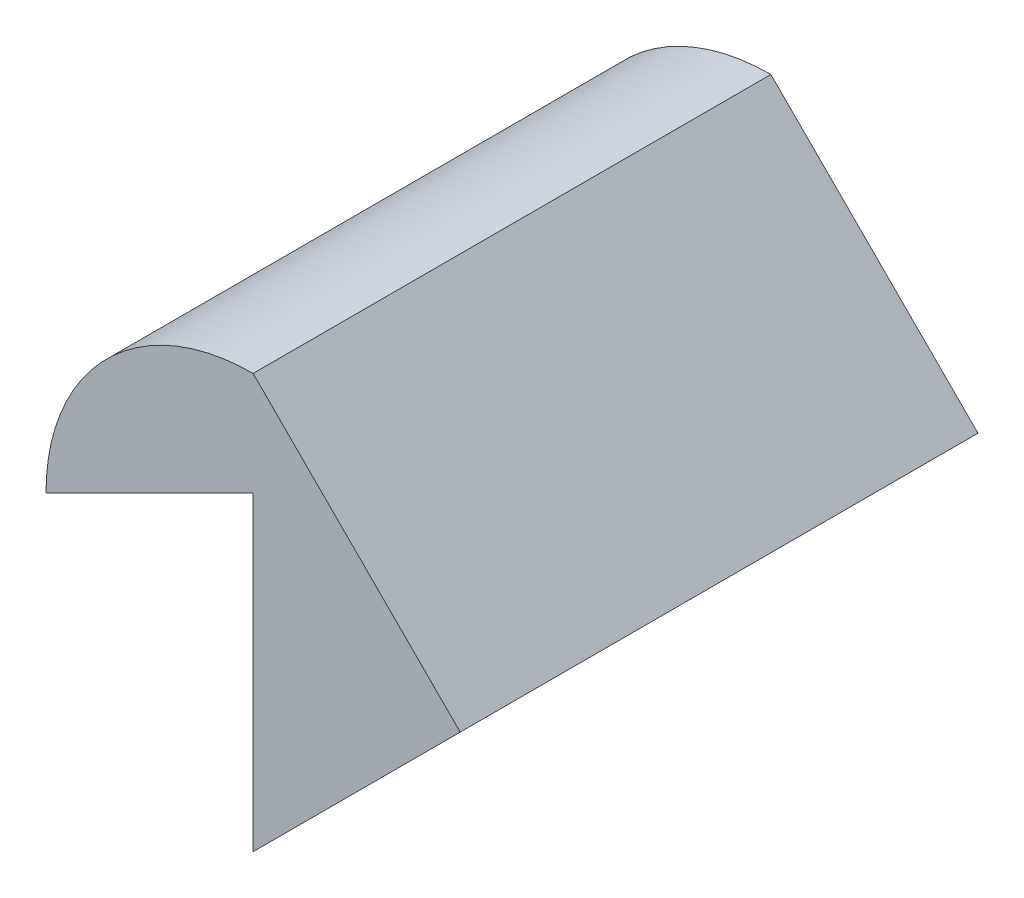
SolidWorks part; units mm, degrees
ref_plane "Front Plane" through (0, 0, 0) normal (0, 0, 1) x (1, 0, 0)
ref_plane "Top Plane" through (0, 0, 0) normal (0, 1, 0) x (1, 0, 0)
ref_plane "Right Plane" through (0, 0, 0) normal (1, 0, 0) x (0, 0, -1)
sketch "Sketch1" plane through (0, 0, 0) normal (0, 0, 1) x (1, 0, 0)
  line L0 (-10, 5) -> (-10, -10)
  line L1 (-10, -10) -> (0, 0)
  line L2 (0, 0) -> (-10, 10)
  line L3 (-10, 5) -> (-20, 0)
  arc A0 (-20, 0) -> (-10, 10) centre (-10, 0) cw
  dimension "D1" = 10
  dimension "D2" = 10
  dimension "D3" = 10
  dimension "D4" = 10
  dimension "D5" = 15
  dimension "D6" = 10
  dimension "D7" = 5
extrude "Boss-Extrude1" add sketch "Sketch1" along normal blind 25
